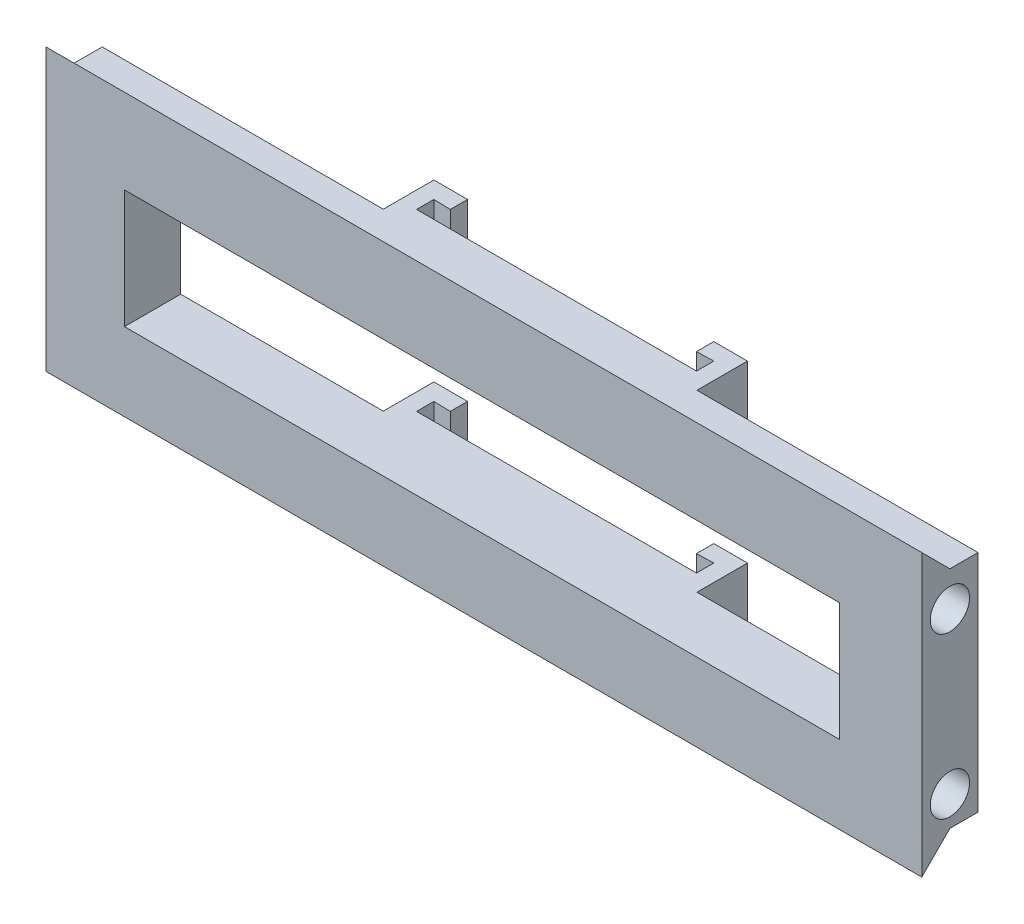
SolidWorks part; units mm, degrees
ref_plane "Front Plane" through (0, 0, 0) normal (0, 0, 1) x (1, 0, 0)
ref_plane "Top Plane" through (0, 0, 0) normal (0, 1, 0) x (1, 0, 0)
ref_plane "Right Plane" through (0, 0, 0) normal (1, 0, 0) x (0, 0, -1)
sketch "Sketch1" plane through (0, 0, 0) normal (0, 1, 0) x (1, 0, 0)
  line L0 (-63.7681, -10.644) -> (-63.7681, -19.644)
  line L1 (-57.7681, -16.7267) -> (-13.9681, -16.7267)
  line L2 (-63.7681, -19.644) -> (-113.7681, -19.644)
  line L3 (-60.7681, -10.644) -> (-57.7681, -10.644)
  line L4 (-7.9681, -10.644) -> (-7.9681, -19.644)
  line L5 (-10.9681, -16.7267) -> (-10.9681, -13.644)
  line L6 (-113.7681, -29.644) -> (42.0319, -29.644)
  line L7 (-10.9681, -10.644) -> (-13.9681, -10.644)
  line L8 (-60.7681, -13.644) -> (-60.7681, -16.7267)
  line L12 (-13.9681, -13.7267) -> (-10.9681, -13.644)
  line L14 (-113.7681, -19.644) -> (-113.7681, -29.644)
  line L17 (-57.7681, -13.7267) -> (-60.7681, -13.644)
  line L21 (42.0319, -19.644) -> (42.0319, -29.644)
  line L22 (-60.7681, -10.644) -> (-57.7681, -10.644)
  line L25 (-7.9681, -19.644) -> (42.0319, -19.644)
  line L26 (-60.7681, -16.7267) -> (-57.7681, -16.7267)
  line L27 (-13.9681, -16.7267) -> (-10.9681, -16.7267)
  line L29 (-13.9681, -10.644) -> (-13.9681, -13.7267)
  line L30 (-57.7681, -10.644) -> (-57.7681, -13.7267)
  line L31 (-60.7681, -10.644) -> (-63.7681, -10.644)
  line L32 (-10.9681, -10.644) -> (-7.9681, -10.644)
  point P24 (-15.8681, -29.644)
extrude "Boss-Extrude1" add sketch "Sketch1" along normal blind 40
sketch "Sketch2" plane through (0, 0, 29.644) normal (0, 0, 1) x (1, 0, 0)
  line L1 (-99.8072, 29.9507) -> (27.4041, 29.9507)
  line L2 (-99.8072, 29.9507) -> (-99.8072, 8.8863)
  line L3 (-99.8072, 8.8863) -> (27.4041, 8.8863)
  line L4 (27.4041, 29.9507) -> (27.4041, 8.8863)
extrude "Cut-Extrude1" cut sketch "Sketch2" against normal blind 60
sketch "Sketch3" plane through (42.0319, 0, 0) normal (1, 0, 0) x (0, 0, -1)
  line L0 (-29.644, 40) -> (-24.644, 40)
  line L1 (-29.644, 40) -> (-29.644, 45)
  line L2 (-19.644, 40) -> (-29.644, 40) construction
  line L3 (-24.644, 40) -> (-29.644, 45)
  line L4 (-29.644, 0) -> (-29.644, -5)
  line L5 (-29.644, -5) -> (-24.644, 0)
  line L6 (-29.644, 0) -> (-24.644, 0)
  line L8 (-19.644, 0) -> (-29.644, 0) construction
extrude "Boss-Extrude2" add sketch "Sketch3" against normal up to surface (155.8 mm away) up to face at (-113.7681, 20, 24.644)
sketch "Sketch4" plane through (42.0319, 0, 0) normal (1, 0, 0) x (0, 0, -1)
  circle A0 centre (-24.644, 33.8062) radius 3.5
  circle A1 centre (-24.644, 5.3036) radius 3.5
extrude "Cut-Extrude2" cut sketch "Sketch4" against normal blind 150
